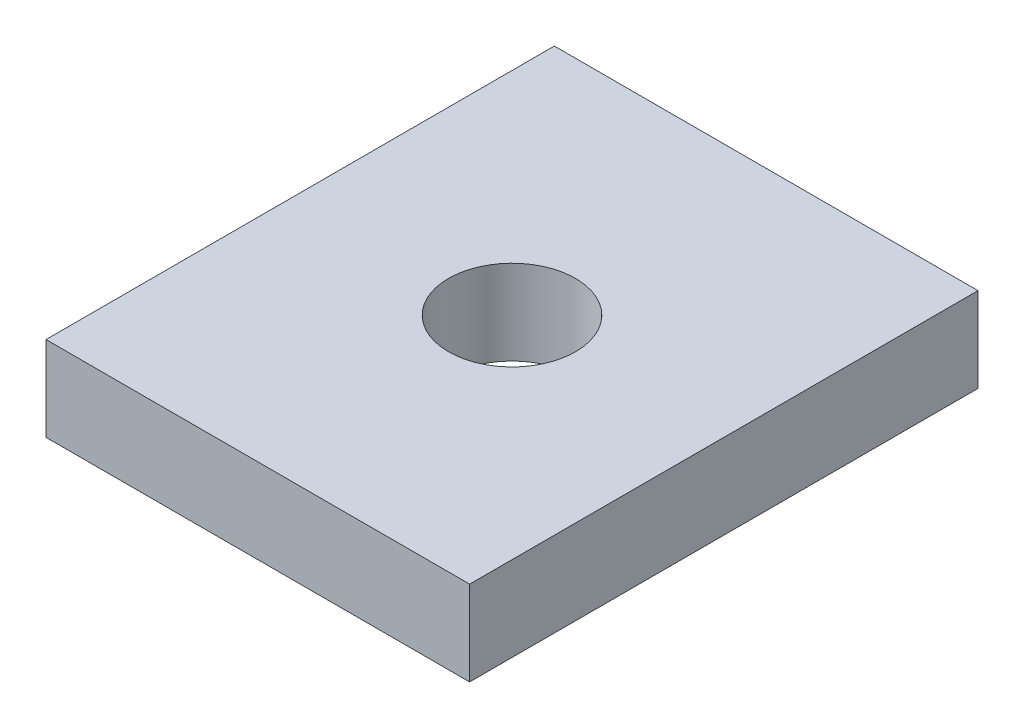
SolidWorks part; units mm, degrees
ref_plane "Front Plane" through (0, 0, 0) normal (0, 0, 1) x (1, 0, 0)
ref_plane "Top Plane" through (0, 0, 0) normal (0, 1, 0) x (1, 0, 0)
ref_plane "Right Plane" through (0, 0, 0) normal (1, 0, 0) x (0, 0, -1)
sketch "Sketch1" plane through (0, 0, 0) normal (0, 1, 0) x (1, 0, 0)
  line L1 (100, 120) -> (-100, 120)
  line L2 (100, 120) -> (100, -120)
  line L3 (100, -120) -> (-100, -120)
  line L4 (-100, 120) -> (-100, -120)
  line L5 (100, 120) -> (-100, -120) construction
  line L6 (100, -120) -> (-100, 120) construction
  point P0 (0, 0)
  dimension "D1" = 200
  dimension "D2" = 240
extrude "base" add sketch "Sketch1" along normal blind 40 contours L1 L4 L3 L2
sketch "Sketch2" plane through (0, 40, 0) normal (0, 1, 0) x (1, 0, 0)
  circle A0 centre (0, 0) radius 30
  dimension "D1" = 60
extrude "actuator cut" cut sketch "Sketch2" against normal blind 40
